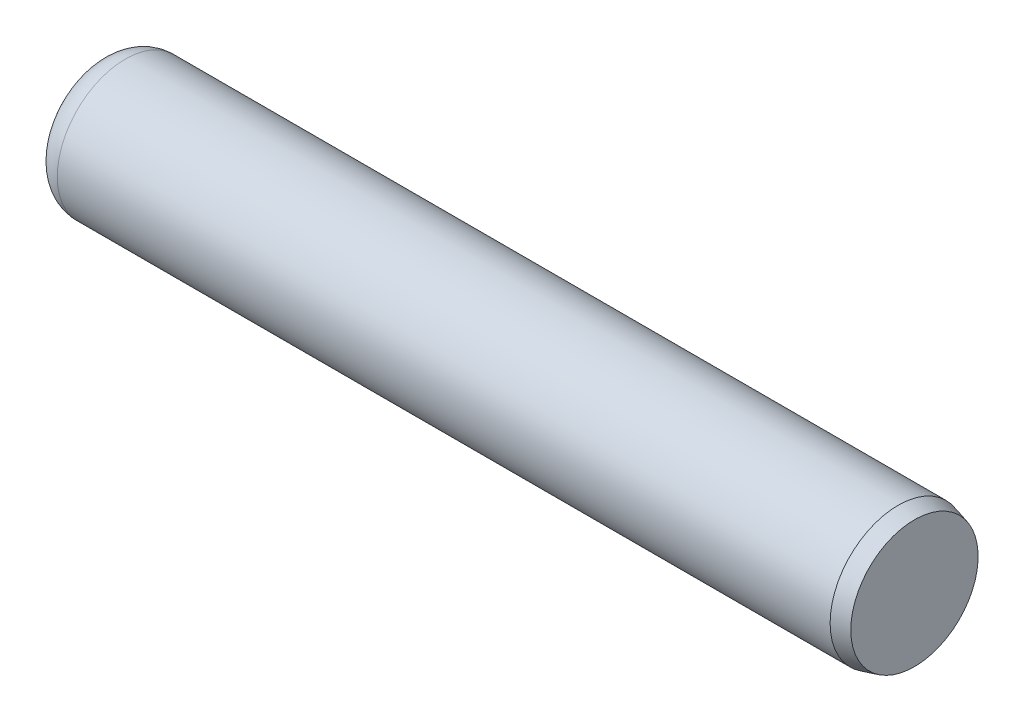
SolidWorks part; units mm, degrees
ref_plane "Plane1" through (0, 0, 0) normal (0, 0, 1) x (1, 0, 0)
ref_plane "Plane2" through (0, 0, 0) normal (0, 1, 0) x (1, 0, 0)
ref_plane "Plane3" through (0, 0, 0) normal (1, 0, 0) x (0, 0, -1)
sketch "Sketch1" plane through (0, 0, 0) normal (0, 0, 1) x (1, 0, 0)
  line L1 (-6.35, 0) -> (107.95, 0) construction
  line L2 (0, 0) -> (4.7625, 0)
  line L3 (4.7625, 0) -> (4.7625, 0.3714)
  line L4 (4.7625, 0.3714) -> (4.6673, 0.3969)
  line L5 (4.6673, 0.3969) -> (0.1588, 0.3969)
  line L6 (0, 0.2381) -> (0, 0)
  arc A0 (0.1588, 0.3969) -> (0, 0.2381) centre (0.1588, 0.2381) ccw
  dimension "D4" = 0.1588
  dimension "D2" = 0.0953
  dimension "D3" = 15
  dimension "Diameter" = 0.7937
  dimension "Length" = 4.7625
revolve "Base-Revolve" add sketch "Sketch1" angle 360 about L1
equation "\"D4@Sketch1\" = \"Diameter@Sketch1\" * 0.2"
equation "\"D2@Sketch1\" = \"Diameter@Sketch1\" * 0.12"
equation "\"D3@Sketch1\" = 15.0"
